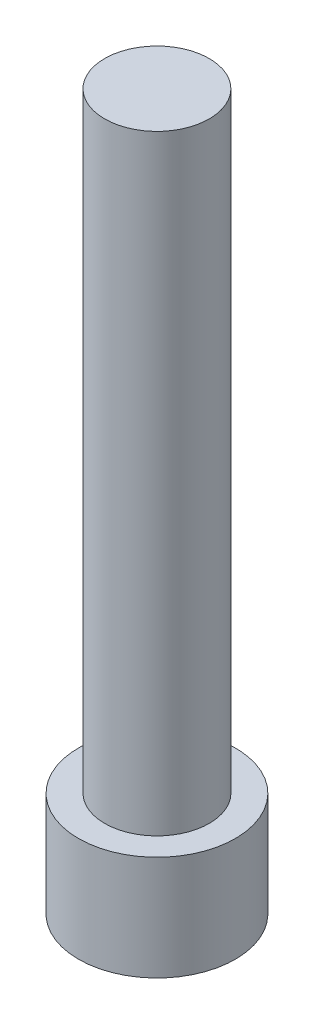
SolidWorks part; units mm, degrees
ref_plane "Front Plane" through (0, 0, 0) normal (0, 0, 1) x (1, 0, 0)
ref_plane "Top Plane" through (0, 0, 0) normal (0, 1, 0) x (1, 0, 0)
ref_plane "Right Plane" through (0, 0, 0) normal (1, 0, 0) x (0, 0, -1)
sketch "Sketch1" plane through (0, 0, 0) normal (0, 1, 0) x (1, 0, 0)
  circle A0 centre (0, 0) radius 9
extrude "Boss-Extrude1" add sketch "Sketch1" along normal blind 12
sketch "Sketch2" plane through (0, 12, 0) normal (0, 1, 0) x (1, 0, 0)
  circle A0 centre (0, 0) radius 6
extrude "Boss-Extrude2" add sketch "Sketch2" along normal blind 70
